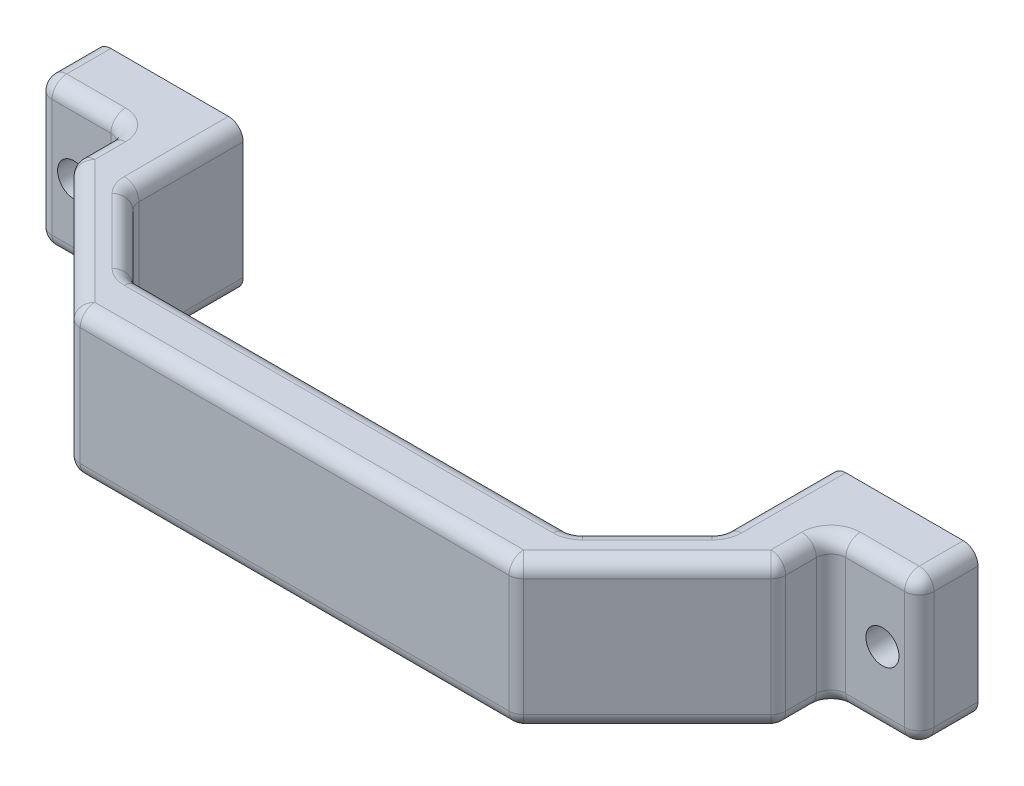
SolidWorks part; units mm, degrees
ref_plane "Front Plane" through (0, 0, 0) normal (0, 0, 1) x (1, 0, 0)
ref_plane "Top Plane" through (0, 0, 0) normal (0, 1, 0) x (1, 0, 0)
ref_plane "Right Plane" through (0, 0, 0) normal (1, 0, 0) x (0, 0, -1)
sketch "Sketch1" plane through (0, 0, 0) normal (0, 0, 1) x (1, 0, 0)
  line L0 (-69.9383, 0) -> (50.0617, 0) construction
  line L2 (-69.9383, -10) -> (-49.9383, -10)
  line L3 (-69.9383, -10) -> (-69.9383, 10)
  line L4 (-69.9383, 10) -> (-49.9383, 10)
  line L5 (-49.9383, -10) -> (-49.9383, 10)
  line L6 (-69.9383, -10) -> (-49.9383, 10) construction
  line L7 (-69.9383, 10) -> (-49.9383, -10) construction
  line L8 (30.0617, -10) -> (50.0617, -10)
  line L9 (30.0617, -10) -> (30.0617, 10)
  line L10 (30.0617, 10) -> (50.0617, 10)
  line L11 (50.0617, -10) -> (50.0617, 10)
  line L12 (30.0617, -10) -> (50.0617, 10) construction
  line L13 (30.0617, 10) -> (50.0617, -10) construction
  circle A0 centre (-64.9383, 0) radius 2.25
  circle A1 centre (45.0617, 0) radius 2.25
  point P3 (-59.9383, 0)
  point P8 (40.0617, 0)
  dimension "D6" = 5
  dimension "D7" = 4.5
  dimension "D8" = 5
  dimension "D9" = 4.5
  dimension "D1" = 20
  dimension "D2" = 20
  dimension "D3" = 20
  dimension "D4" = 20
  dimension "D5" = 80
extrude "Boss-Extrude1" add sketch "Sketch1" along normal blind 8
sketch "Sketch2" plane through (0, -10, 0) normal (0, -1, 0) x (1, 0, 0)
  line L0 (-69.9383, 0) -> (-49.9383, 0) construction
  line L1 (-39.9383, 25) -> (20.0617, 25)
  line L3 (-39.9383, 33) -> (20.0617, 33)
  line L7 (-39.9383, 25) -> (-49.9383, 15)
  line L8 (-49.9383, 15) -> (-49.9383, 8)
  line L9 (-49.9383, 8) -> (-57.9383, 8)
  line L10 (-69.9383, 8) -> (-49.9383, 8) construction
  line L11 (-57.9383, 8) -> (-57.9383, 15)
  line L12 (-57.9383, 15) -> (-39.9383, 33)
  line L13 (-9.9383, 33) -> (-9.9383, 4.7609) construction
  line L14 (20.0617, 25) -> (30.0617, 15)
  line L15 (30.0617, 15) -> (30.0617, 8)
  line L16 (30.0617, 8) -> (38.0617, 8)
  line L17 (38.0617, 8) -> (38.0617, 15)
  line L18 (38.0617, 15) -> (20.0617, 33)
  dimension "D1" = 25
  dimension "D2" = 8
  dimension "D5" = 135
  dimension "D6" = 7
extrude "Boss-Extrude2" add sketch "Sketch2" against normal through all
fillet "Fillet2" radius 2 40 edges at (44.0617, 10, 8) (44.0617, -10, 8) (-63.9383, 10, 8) (-63.9383, -10, 8) (30.0617, 10, 7.5) (25.0617, -10, 20) (25.0617, 10, 20) (30.0617, 0, 15) (20.0617, 0, 25) (-9.9383, -10, 25) (-9.9383, 10, 25) (-44.9383, -10, 20) (-44.9383, 10, 20) (-49.9383, 10, 7.5) (-49.9383, 0, 15) (-39.9383, 0, 25) (-49.9383, -10, 7.5) (30.0617, -10, 7.5) (38.0617, -10, 11.5) (38.0617, 10, 11.5) (38.0617, 0, 8) (38.0617, 0, 15) (29.0617, -10, 24) (29.0617, 10, 24) (20.0617, 0, 33) (-9.9383, -10, 33) (-9.9383, 10, 33) (-39.9383, 0, 33) (-48.9383, -10, 24) (-48.9383, 10, 24) (-57.9383, 0, 15) (-57.9383, -10, 11.5) (-57.9383, 10, 11.5) (-57.9383, 0, 8) (50.0617, -10, 4) (50.0617, 0, 8) (50.0617, 10, 4) (-69.9383, -10, 4) (-69.9383, 0, 8) (-69.9383, 10, 4)
